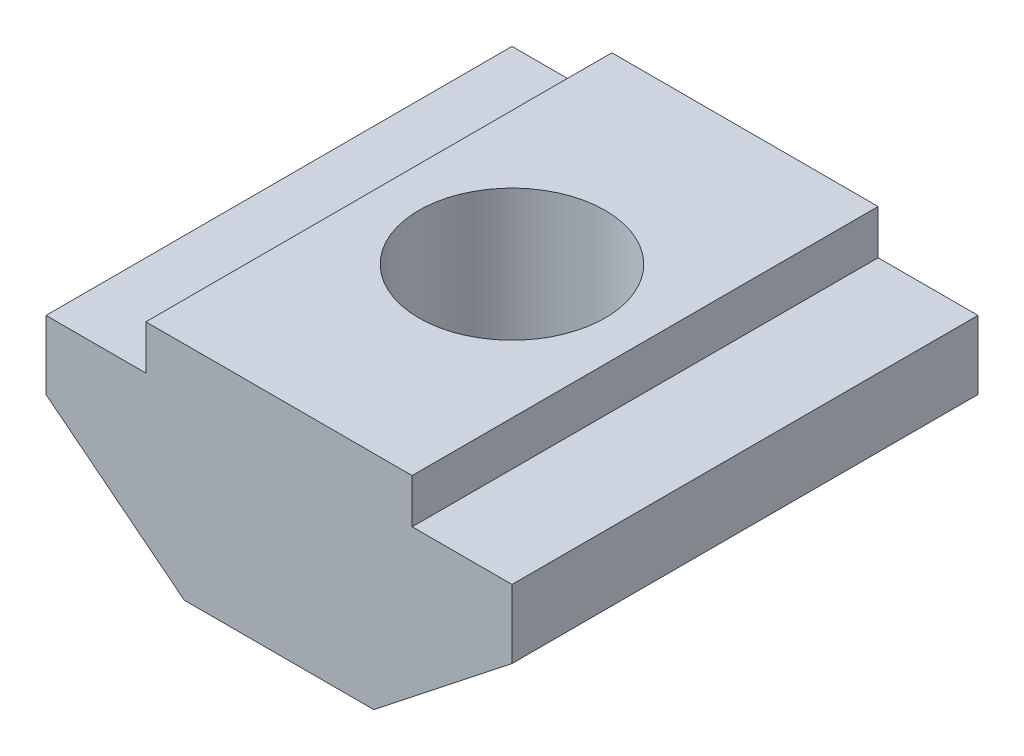
SolidWorks part; units mm, degrees
ref_plane "Front" through (0, 0, 0) normal (0, 0, 1) x (1, 0, 0)
ref_plane "Top" through (0, 0, 0) normal (0, 1, 0) x (1, 0, 0)
ref_plane "Right" through (0, 0, 0) normal (1, 0, 0) x (0, 0, -1)
sketch "Sketch1" plane through (0, 0, 0) normal (0, 0, 1) x (1, 0, 0)
  line L0 (0, 0) -> (0, 5) construction
  line L1 (-3, 5) -> (3, 5)
  line L2 (3, 5) -> (3, 4)
  line L3 (3, 4) -> (5.25, 4)
  line L4 (5.25, 4) -> (5.25, 2.4559)
  line L5 (5.25, 2.4559) -> (2.1356, 0)
  line L6 (2.1356, 0) -> (-2.1356, 0)
  line L7 (-5.25, 2.4559) -> (-2.1356, 0)
  line L8 (-5.25, 4) -> (-5.25, 2.4559)
  line L9 (-3, 4) -> (-5.25, 4)
  line L10 (-3, 5) -> (-3, 4)
  dimension "D1" = 1
  dimension "D2" = 6
  dimension "D3" = 5
  dimension "D4" = 10.5
extrude "Boss-Extrude1" add sketch "Sketch1" along normal blind 10.5
hole_wizard "M5x0.8 Tapped Hole1" positions "Sketch2" profile "Sketch3" tap size "M5x0.8" standard "ANSI Metric" end condition through all
sketch "Sketch2" plane through (0, 5, 0) normal (0, 1, 0) x (1, 0, 0)
  line L0 (0, 0) -> (0, -10.5) construction
  line L1 (3, -10.5) -> (-3, -10.5) construction
  point P0 (0, -5.25)
  point P12 (0, -5.25)
sketch "Sketch3" plane through (0, 5, 5.25) normal (1, 0, 0) x (0, 0, 1)
  line L0 (0, 0) -> (0, 5)
  line L1 (0, 5) -> (2.1, 5)
  line L2 (2.1, 5) -> (2.1, 0)
  line L5 (2.1, 0) -> (0, 0)
  line L11 (0, -6.35) -> (0, 107.95) construction
  dimension "Thru Tap Drill Dia." = 4.2
  dimension "Thru Tap Drill Depth" = 5
cosmetic thread "Hole Thread1"
